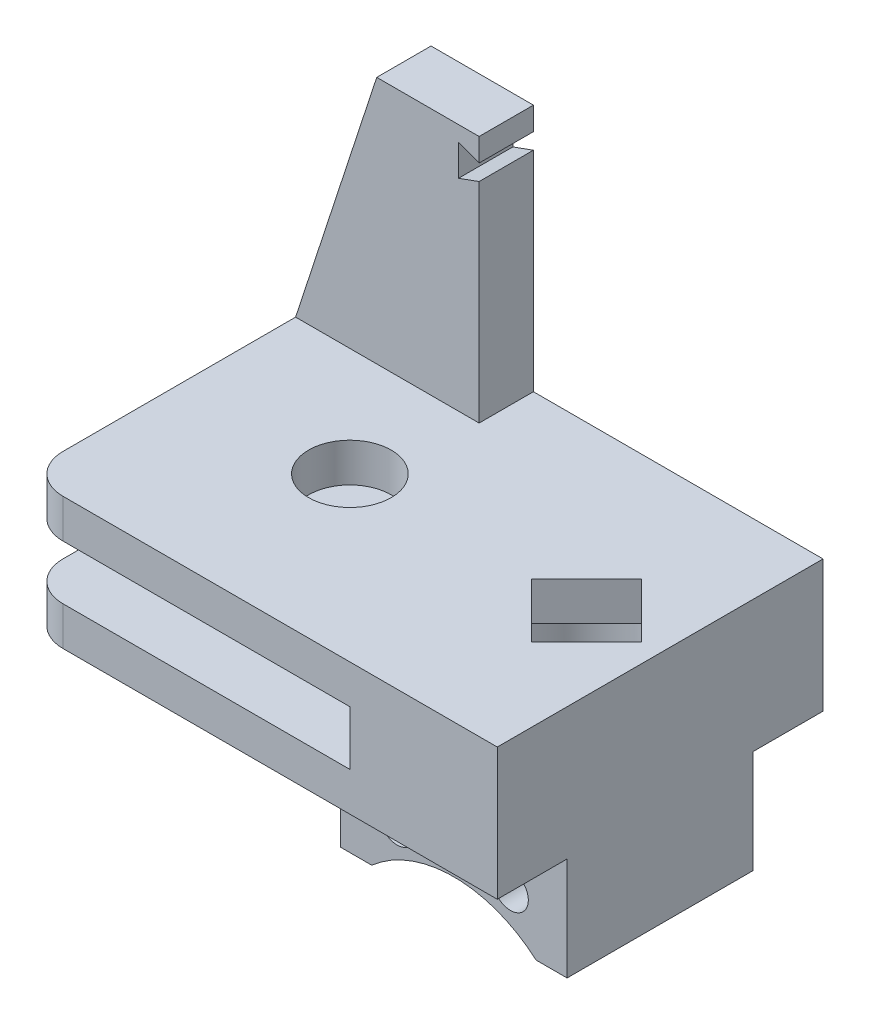
SolidWorks part; units mm, degrees
ref_plane "Front Plane" through (0, 0, 0) normal (0, 0, 1) x (1, 0, 0)
ref_plane "Top Plane" through (0, 0, 0) normal (0, 1, 0) x (1, 0, 0)
ref_plane "Right Plane" through (0, 0, 0) normal (1, 0, 0) x (0, 0, -1)
sketch "Sketch1" plane through (0, 0, 0) normal (0, 1, 0) x (1, 0, 0)
  line L0 (0, -13.335) -> (25.4, -13.335)
  line L1 (0, 13.335) -> (25.4, 13.335)
  line L2 (25.4, 13.335) -> (25.4, -13.335)
  circle A0 centre (0, 0) radius 12.7 construction
  circle A1 centre (0, 0) radius 13.335 construction
  circle A2 centre (0, 0) radius 3.3782
  arc A3 (11.5484, 6.6675) -> (11.5484, -6.6675) centre (0, 0) ccw construction
  arc A4 (0, 13.335) -> (0, -13.335) centre (0, 0) ccw
  dimension "D1" = 25.4
  dimension "D2" = 0.635
  dimension "D4" = 6.7564
  dimension "D3" = 25.4
extrude "Boss-Extrude1" add sketch "Sketch1" along normal blind 3.175
sketch "Sketch2" plane through (0, 0, 0) normal (0, -1, 0) x (-1, 0, 0)
  line L3 (-25.4, 13.335) -> (-25.4, -13.335)
  line L5 (-13.335, 0) -> (-13.335, 13.335)
  line L6 (-25.4, 13.335) -> (-13.335, 13.335)
  line L7 (-13.335, 0) -> (-13.335, -13.335)
  line L8 (0, -13.335) -> (-25.4, -13.335) construction
  line L9 (-13.335, -13.335) -> (-25.4, -13.335)
  arc A3 (0, 13.335) -> (0, -13.335) centre (0, 0) ccw construction
extrude "Boss-Extrude2" add sketch "Sketch2" along normal blind 4.445 contours L3 L9 L7 L5 L6
ref_plane "Plane2" through (0, -2.2225, 0) normal (0, -1, 0) x (-1, 0, 0)
mirror "Mirror2" about plane through (0, -2.2225, 0) normal (0, -1, 0) of "Boss-Extrude1"
sketch "Sketch7" plane through (0, -7.62, 0) normal (0, -1, 0) x (-1, 0, 0)
  line L0 (-25.4, 13.335) -> (-25.4, 7.62) construction
  line L1 (-25.4, 13.335) -> (-25.4, -13.335) construction
  line L2 (0, 0) -> (-25.4, 0) construction
  line L3 (-25.4, -13.335) -> (-25.4, -7.62) construction
  line L5 (-25.4, 7.62) -> (-6.858, 7.62)
  line L6 (-25.4, 7.62) -> (-25.4, -7.62)
  line L7 (-25.4, -7.62) -> (-6.858, -7.62)
  line L8 (-6.858, 7.62) -> (-6.858, -7.62)
  dimension "D1" = 5.715
  dimension "D2" = 18.542
extrude "Boss-Extrude4" add sketch "Sketch7" along normal blind 8.4391
sketch "Sketch8" plane through (0, 0, -7.62) normal (0, 0, -1) x (-1, 0, 0)
  line L0 (-16.129, -7.62) -> (-16.129, -16.0591) construction
  line L1 (-16.129, -16.0591) -> (-25.4, -16.0591) construction
  line L2 (-20.7645, -16.0591) -> (-20.7645, -7.62) construction
  line L3 (-6.858, -7.62) -> (-25.4, -7.62) construction
  line L4 (-6.858, -16.0591) -> (-25.4, -16.0591) construction
  line L5 (0, -7.62) -> (-25.4, -7.62) construction
  circle A0 centre (-20.7645, -12.1285) radius 1.4605
  circle A1 centre (-11.4935, -12.1285) radius 1.4605
  dimension "D1" = 2.921
  dimension "D2" = 4.5085
extrude "Cut-Extrude3" cut sketch "Sketch8" against normal through all
sketch "Sketch9" plane through (0, 0, -7.62) normal (0, 0, -1) x (-1, 0, 0)
  line L0 (-16.129, -16.0591) -> (-16.129, -23.6791) construction
  line L1 (-6.858, -16.0591) -> (-25.4, -16.0591) construction
  line L2 (-16.129, -16.0591) -> (-16.129, -13.5191) construction
  circle A0 centre (-16.129, -23.6791) radius 10.16
  dimension "D1" = 2.54
  dimension "D2" = 7.62
extrude "Cut-Extrude4" cut sketch "Sketch9" against normal through all
sketch "Sketch22" plane through (0, 3.175, 0) normal (0, 1, 0) x (1, 0, 0)
  line L0 (25.4, 0) -> (19.3675, 0) construction
  line L1 (25.4, 13.335) -> (25.4, -13.335) construction
  line L2 (21.6126, 2.2451) -> (19.3675, 4.4901) construction
  line L3 (17.1224, -2.2451) -> (21.6126, -2.2451) construction
  line L4 (17.1224, -2.2451) -> (17.1224, 2.2451) construction
  line L5 (17.1224, 2.2451) -> (21.6126, 2.2451) construction
  line L6 (21.6126, -2.2451) -> (21.6126, 2.2451) construction
  line L7 (17.1224, -2.2451) -> (21.6126, 2.2451) construction
  line L8 (17.1224, 2.2451) -> (21.6126, -2.2451) construction
  line L9 (19.3675, 4.4901) -> (17.1224, 2.2451) construction
  line L10 (19.3675, -4.4901) -> (23.8576, 0.024)
  line L11 (19.3675, -4.4901) -> (14.8774, -0.024)
  line L12 (23.8576, 0.024) -> (19.3675, 4.4901)
  line L13 (14.8774, -0.024) -> (19.3675, 4.4901)
  line L14 (19.3675, -4.4901) -> (19.3675, 4.4901) construction
  line L15 (23.8576, 0.024) -> (14.8774, -0.024) construction
  dimension "D1" = 6.0325
  dimension "D2" = 6.35
extrude "Cut-Extrude6" cut sketch "Sketch22" against normal blind 9.525
sketch "Sketch23" plane through (0, -6.35, 0) normal (0, 1, 0) x (1, 0, 0)
  line L4 (14.8774, -0.024) -> (23.8576, 0.024) construction
  circle A1 centre (19.3675, 0) radius 4.4901
extrude "Cut-Extrude7" cut sketch "Sketch23" along normal blind 6.35
sketch "Sketch16" plane through (0, 3.175, 0) normal (0, 1, 0) x (1, 0, 0)
  line L0 (0, 13.335) -> (-13.335, 0) construction
  line L1 (0, 13.335) -> (-13.335, 13.335)
  line L2 (0, 13.335) -> (0, 0) construction
  line L3 (0, 0) -> (-13.335, 0) construction
  line L4 (-13.335, 13.335) -> (-13.335, 0)
  line L5 (0, -13.335) -> (-13.335, 0) construction
  line L6 (0, -13.335) -> (-13.335, -13.335)
  line L7 (-13.335, -13.335) -> (-13.335, 0)
  line L8 (-6.6675, 6.6675) -> (-6.6675, -6.6675)
  line L9 (-6.6675, -6.6675) -> (0, -13.335)
  line L10 (-6.6675, 6.6675) -> (0, 13.335)
  arc A0 (0, 13.335) -> (0, -13.335) centre (0, 0) ccw construction
extrude "Boss-Extrude10" add sketch "Sketch16" against normal up to surface (3.175 mm away) up to face at (0, 0, 3.3782)
sketch "Sketch17" plane through (0, -7.62, 0) normal (0, -1, 0) x (1, 0, 0)
  line L0 (-13.335, -13.335) -> (-13.335, 0)
  line L1 (-13.335, 0) -> (0, -13.335) construction
  line L2 (0, -13.335) -> (-13.335, -13.335)
  line L3 (-13.335, 0) -> (0, 13.335) construction
  line L4 (0, 13.335) -> (-13.335, 13.335)
  line L5 (-13.335, 13.335) -> (-13.335, 0)
  line L6 (-6.6675, 6.6675) -> (-6.6675, -6.6675)
  line L7 (-6.6675, -6.6675) -> (0, -13.335)
  line L8 (-6.6675, 6.6675) -> (0, 13.335)
  arc A0 (0, 13.335) -> (0, -13.335) centre (0, 0) ccw construction
extrude "Boss-Extrude11" add sketch "Sketch17" against normal up to surface (3.175 mm away) up to face at (0, -4.445, 3.3782)
sketch "Sketch19" plane through (0, 3.175, 0) normal (0, 1, 0) x (1, 0, 0)
  line L0 (0, 0) -> (0, 13.335) construction
  line L1 (-13.335, 13.335) -> (25.4, 13.335) construction
  line L2 (3.3782, 0) -> (3.3782, 13.335) construction
  line L3 (3.3782, 13.335) -> (0, 13.335) construction
  line L5 (1.6891, 13.335) -> (-6.6929, 13.335)
  line L6 (1.6891, 13.335) -> (1.6891, 8.89)
  line L7 (1.6891, 8.89) -> (-6.6929, 8.89)
  line L8 (-6.6929, 13.335) -> (-6.6929, 8.89)
  circle A0 centre (0, 0) radius 3.3782 construction
  dimension "D1" = 8.382
  dimension "D2" = 4.445
extrude "Boss-Extrude12" add sketch "Sketch19" along normal blind 20.32
sketch "Sketch20" plane through (0, 0, -8.89) normal (0, 0, 1) x (1, 0, 0)
  line L0 (-6.6929, 23.495) -> (-13.335, 3.175)
  line L1 (-13.335, 3.175) -> (-6.6929, 3.175)
  line L2 (-6.6929, 3.175) -> (-6.6929, 23.495)
  point P4 (0, 0)
extrude "Boss-Extrude13" add sketch "Sketch20" against normal up to surface (4.445 mm away) up to face at (1.1769, 2.9633, -13.335)
sketch "Sketch21" plane through (0, 0, -8.89) normal (0, 0, 1) x (1, 0, 0)
  line L0 (0, 3.175) -> (0, 23.495) construction
  line L1 (3.3782, 3.175) -> (-3.3782, 3.175) construction
  line L2 (-6.6929, 23.495) -> (1.6891, 23.495) construction
  line L3 (0, 22.225) -> (1.6891, 21.6102)
  line L4 (1.6891, 23.495) -> (1.6891, 3.175) construction
  line L5 (1.6891, 21.6102) -> (1.6891, 20.2998)
  line L7 (0, 22.225) -> (0, 19.685)
  line L8 (0, 19.685) -> (1.6891, 20.2998)
  point P11 (1.6891, 22.86)
  point P13 (1.6891, 22.86)
  point P16 (1.6891, 19.8102)
  point P17 (1.6891, 22.86)
  point P18 (1.6891, 21.8848)
  dimension "D1" = 70
  dimension "D2" = 70
  dimension "D3" = 1.27
  dimension "D4" = 2.54
extrude "Cut-Extrude5" cut sketch "Sketch21" against normal blind 12.7
fillet "Fillet2" radius 3.175 2 edges at (-13.335, -6.0325, 13.335) (-13.335, 1.5875, 13.335)
